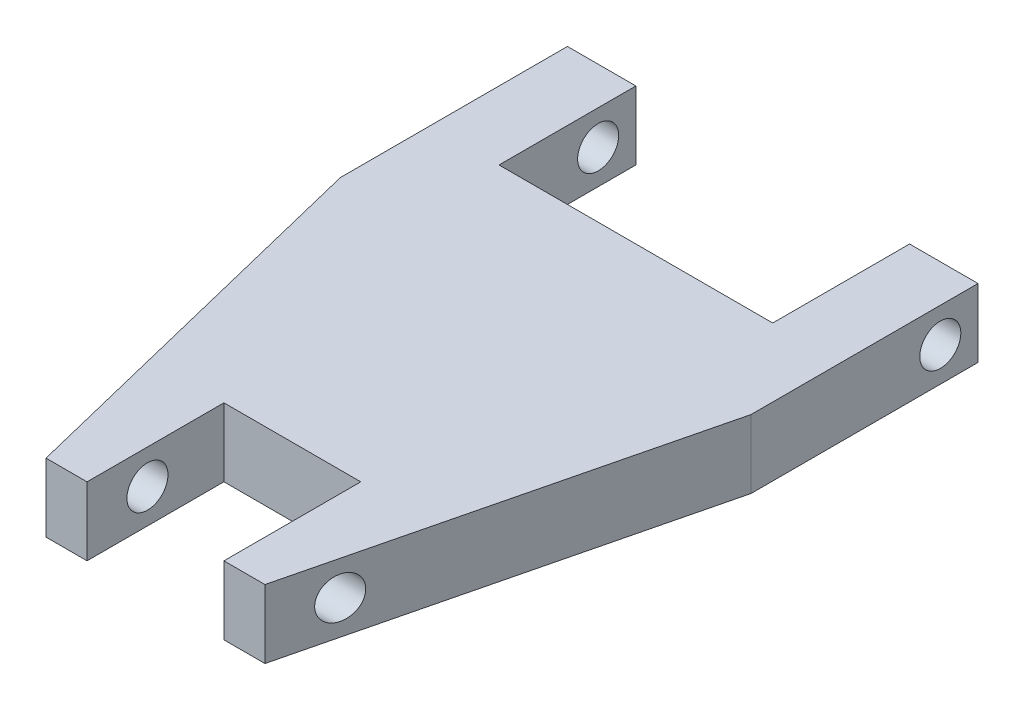
SolidWorks part; units mm, degrees
material "1060 Alloy"
ref_plane "Front Plane" through (0, 0, 0) normal (0, 0, 1) x (1, 0, 0)
ref_plane "Top Plane" through (0, 0, 0) normal (0, 1, 0) x (1, 0, 0)
ref_plane "Right Plane" through (0, 0, 0) normal (1, 0, 0) x (0, 0, -1)
sketch "Sketch1" plane through (0, 0, 0) normal (0, 1, 0) x (1, 0, 0)
  line L0 (-19.05, 28.623) -> (-19.05, 7.56)
  line L5 (-12.7, 15.923) -> (12.7, 15.923)
  line L6 (-19.05, 7.56) -> (-10.16, -28.6558)
  line L8 (-12.7, 28.623) -> (-12.7, 15.923)
  line L12 (-6.35, -28.6558) -> (-6.35, -15.9558)
  line L15 (0, 28.6312) -> (0, -28.6312) construction
  line L16 (-12.7, 28.623) -> (-19.05, 28.623)
  line L17 (-10.16, -28.6558) -> (-6.35, -28.6558)
  line L21 (-6.35, -15.9558) -> (6.35, -15.9558)
  line L22 (6.35, -28.6558) -> (6.35, -15.9558)
  line L23 (10.16, -28.6558) -> (6.35, -28.6558)
  line L24 (19.05, 7.56) -> (10.16, -28.6558)
  line L25 (19.05, 28.623) -> (19.05, 7.56)
  line L26 (12.7, 28.623) -> (19.05, 28.623)
  line L27 (12.7, 28.623) -> (12.7, 15.923)
  point P0 (0, 0)
  point P11 (0, -15.9558)
  point P20 (0, 15.923)
  point P21 (0, 15.923)
  point P23 (0, -15.9558)
  dimension "D1" = 12.7
  dimension "D2" = 25.4
  dimension "D3" = 6.35
  dimension "D4" = 3.81
  dimension "D5" = 12.7
  dimension "D6" = 12.7
extrude "Boss-Extrude1" add sketch "Sketch1" along normal mid plane 6.35
sketch "Sketch2" plane through (0, 0, 0) normal (-1, 0, 0) x (0, 0, 1)
  line L1 (0, 0) -> (-25.1222, 0) construction
  line L2 (0, 0) -> (23.0498, 0) construction
  circle A2 centre (-25.1222, 0) radius 1.905
  circle A3 centre (23.0498, 0) radius 1.905
  dimension "D1" = 3.81
  dimension "D2" = 3.81
extrude "Cut-Extrude1" cut sketch "Sketch2" against normal through all both and the other way through all
